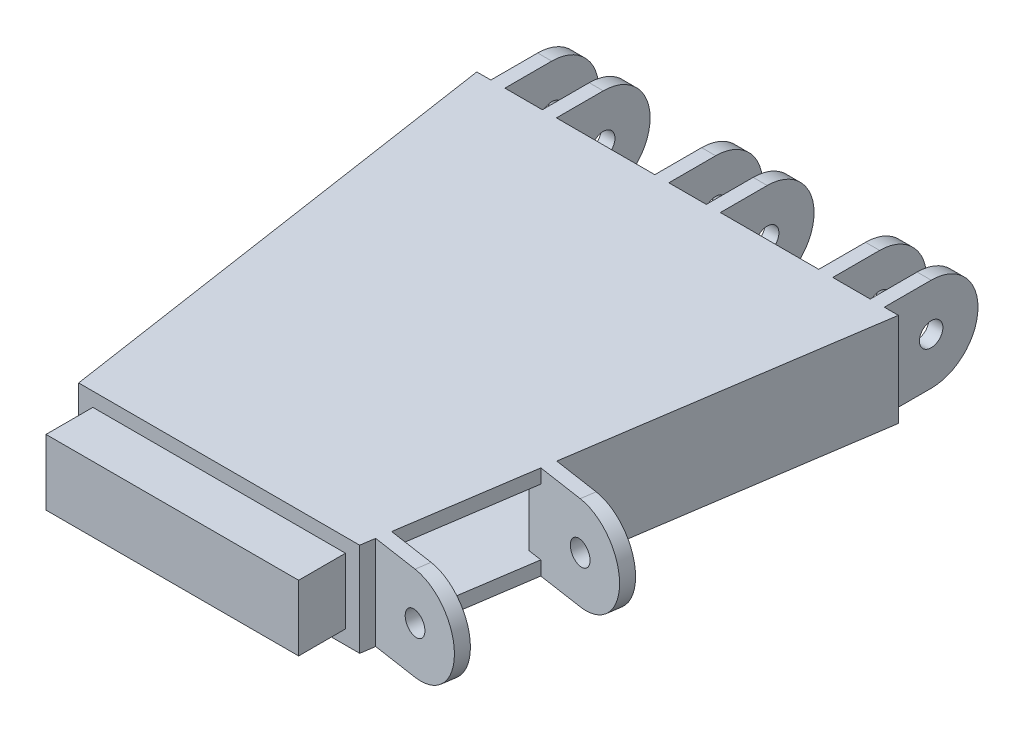
SolidWorks part; units mm, degrees
ref_plane "Front Plane" through (0, 0, 0) normal (0, 0, 1) x (1, 0, 0)
ref_plane "Top Plane" through (0, 0, 0) normal (0, 1, 0) x (1, 0, 0)
ref_plane "Right Plane" through (0, 0, 0) normal (1, 0, 0) x (0, 0, -1)
sketch "Sketch1" plane through (0, 0, 0) normal (0, 1, 0) x (1, 0, 0)
  line L0 (-45, 0) -> (45, 0)
  line L1 (45, 0) -> (30, -100)
  line L2 (30, -100) -> (-30, -100)
  line L3 (-30, -100) -> (-45, 0)
  point P2 (0, 0)
  dimension "D1" = 60
  dimension "D3" = 90
  dimension "D4" = 100
extrude "Boss-Extrude1" add sketch "Sketch1" along normal mid plane 20
sketch "Sketch2" plane through (0, 0, 0) normal (1, 0, 0) x (0, 0, -1)
  line L0 (0, 10) -> (0, -10) construction
  line L1 (0, -10) -> (-100, -10) construction
  line L2 (0, 10) -> (0, -10) construction
  line L3 (0, -10) -> (-100, -10) construction
  line L5 (0, 10) -> (10, 10)
  line L6 (0, 10) -> (0, -10)
  line L7 (0, -10) -> (10, -10)
  arc A0 (10, -10) -> (10, 10) centre (10, 0) ccw
  circle A1 centre (10, 0) radius 2.5
  dimension "D2" = 10
  dimension "D3" = 5
  dimension "D1" = 10
extrude "Boss-Extrude2" add sketch "Sketch2" along normal mid plane 14 from offset 35
pattern_linear "LPattern1" count 3 spacing 35 along (-1, 0, 0) of "Boss-Extrude2"
shell "Shell1" thickness 3
sketch "Sketch3" plane through (0, 0, 0) normal (0, 0, 1) x (1, 0, 0)
  line L0 (-42, 10) -> (-42, -10) construction
  line L1 (-42, -10) -> (-45, -10) construction
  line L2 (-45, -10) -> (-45, 10) construction
  line L3 (-45, 10) -> (-42, 10) construction
  line L4 (42, -10) -> (42, 10) construction
  line L5 (42, 10) -> (45, 10) construction
  line L6 (45, 10) -> (45, -10) construction
  line L7 (45, -10) -> (42, -10) construction
  line L8 (28, -10) -> (7, -10) construction
  line L9 (28, 10) -> (7, 10) construction
  line L10 (-7, 10) -> (-28, 10) construction
  line L11 (-7, -10) -> (-28, -10) construction
  line L12 (-45, 10) -> (-45, -10) construction
  line L13 (-42, 10) -> (-45, 10) construction
  line L14 (45, 10) -> (42, 10) construction
  line L15 (-42, 10) -> (-42, -10) construction
  line L16 (-42, -10) -> (-45, -10) construction
  line L17 (-45, -10) -> (-45, 10) construction
  line L18 (-45, 10) -> (-42, 10) construction
  line L19 (42, -10) -> (42, 10) construction
  line L20 (42, 10) -> (45, 10) construction
  line L21 (45, 10) -> (45, -10) construction
  line L22 (45, -10) -> (42, -10) construction
  line L23 (28, -10) -> (7, -10) construction
  line L24 (28, 10) -> (7, 10) construction
  line L25 (-7, 10) -> (-28, 10) construction
  line L26 (-7, -10) -> (-28, -10) construction
  line L27 (-45, 10) -> (-45, -10) construction
  line L28 (-42, 10) -> (-45, 10) construction
  line L29 (45, 10) -> (42, 10) construction
  line L31 (42, 10) -> (28, 10) construction
  line L32 (42, 10) -> (42, -10) construction
  line L33 (42, -10) -> (28, -10) construction
  line L34 (28, 10) -> (28, -10) construction
  line L35 (7, 10) -> (-7, 10) construction
  line L36 (7, 10) -> (7, -10) construction
  line L37 (7, -10) -> (-7, -10) construction
  line L38 (-7, 10) -> (-7, -10) construction
  line L39 (-28, 10) -> (-42, 10) construction
  line L40 (-28, 10) -> (-28, -10) construction
  line L41 (-28, -10) -> (-42, -10) construction
  line L42 (-42, 10) -> (-42, -10) construction
  line L43 (39, 10) -> (31, 10)
  line L44 (39, 10) -> (39, -10)
  line L45 (39, -10) -> (31, -10)
  line L46 (31, 10) -> (31, -10)
  line L47 (4, 10) -> (-4, 10)
  line L48 (4, 10) -> (4, -10)
  line L49 (4, -10) -> (-4, -10)
  line L50 (-4, 10) -> (-4, -10)
  line L51 (-31, 10) -> (-39, 10)
  line L52 (-31, 10) -> (-31, -10)
  line L53 (-31, -10) -> (-39, -10)
  line L54 (-39, 10) -> (-39, -10)
  dimension "D1" = 3
  dimension "D2" = 3
  dimension "D3" = 3
  dimension "D4" = 3
  dimension "D5" = 3
  dimension "D6" = 3
extrude "Cut-Extrude1" cut sketch "Sketch3" against normal blind 20
ref_plane "thumb plane" through (-14.0098, 0, 93.3985) normal (-0.1483, 0, 0.9889) x (0.9889, 0, 0.1483)
sketch "Sketch5" plane through (-14.0098, 0, 93.3985) normal (-0.1483, 0, 0.9889) x (0.9889, 0, 0.1483)
  line L0 (44.5021, 10) -> (44.5021, -10) construction
  line L1 (44.5021, 10) -> (44.5021, -10) construction
  line L3 (44.5021, 10) -> (54.5021, 10)
  line L4 (44.5021, 10) -> (44.5021, -10)
  line L5 (44.5021, -10) -> (54.5021, -10)
  arc A0 (54.5021, -10) -> (54.5021, 10) centre (54.5021, 0) ccw
  circle A1 centre (54.5021, 0) radius 2.5
  dimension "D2" = 5
  dimension "D1" = 10
extrude "Boss-Extrude3" add sketch "Sketch5" against normal blind 3 from offset 3 offset against normal yes
pattern_linear "LPattern2" count 2 spacing 31 along (0.1483, 0, -0.9889) of "Boss-Extrude3"
sketch "Sketch6" plane through (44.0098, 0, 6.6015) normal (0.9889, 0, 0.1483) x (0.1483, 0, -0.9889)
  line L0 (-88.4434, 10) -> (-88.4434, -10) construction
  line L1 (-88.4434, 7) -> (-60.4434, 7)
  line L2 (-88.4434, 7) -> (-88.4434, -7)
  line L3 (-88.4434, -7) -> (-60.4434, -7)
  line L4 (-60.4434, 7) -> (-60.4434, -7)
  line L5 (-60.4434, 10) -> (-60.4434, -10) construction
  line L6 (-88.4434, 10) -> (-60.4434, 10) construction
  line L7 (-88.4434, -10) -> (-60.4434, -10) construction
  dimension "D1" = 3
  dimension "D2" = 3
extrude "Cut-Extrude2" cut sketch "Sketch6" against normal blind 3
sketch "Sketch7" plane through (0, 0, 100) normal (0, 0, 1) x (1, 0, 0)
  line L1 (-26.9664, 7) -> (26.9664, 7)
  line L2 (-26.9664, 7) -> (-26.9664, -7)
  line L3 (-26.9664, -7) -> (26.9664, -7)
  line L4 (26.9664, 7) -> (26.9664, -7)
extrude "Boss-Extrude4" add sketch "Sketch7" along normal blind 10 separate body
